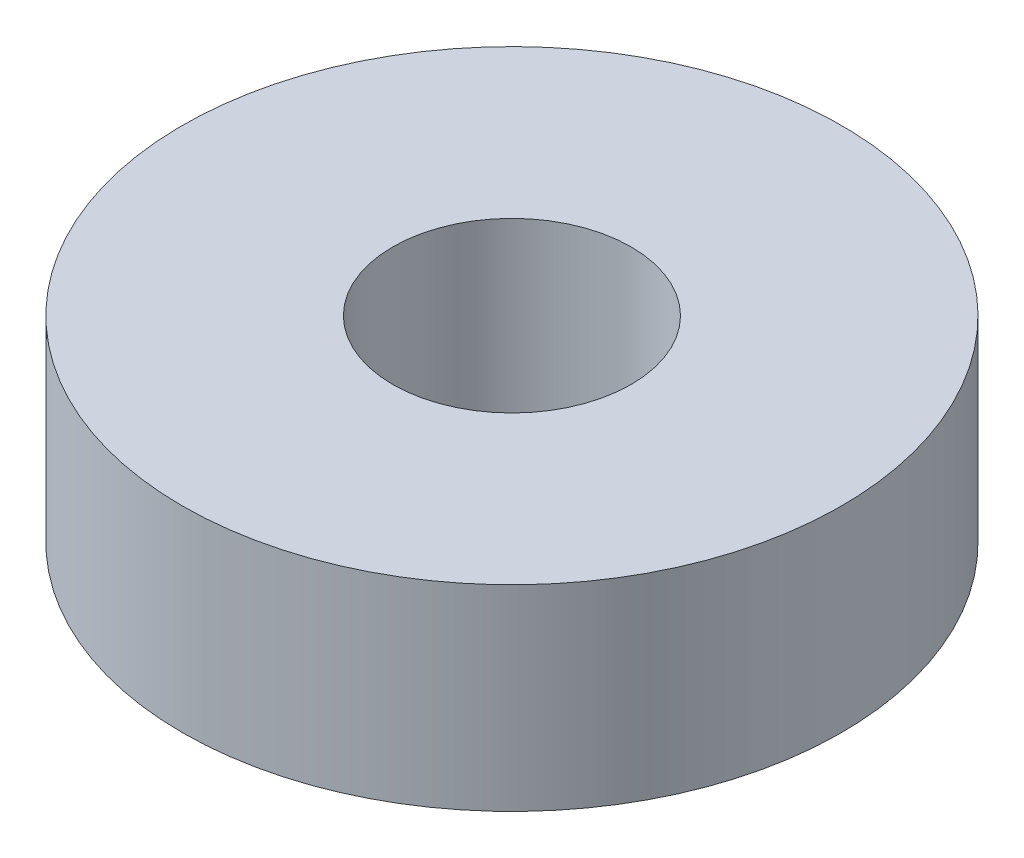
SolidWorks part; units mm, degrees
ref_plane "Front Plane" through (0, 0, 0) normal (0, 0, 1) x (1, 0, 0)
ref_plane "Top Plane" through (0, 0, 0) normal (0, 1, 0) x (1, 0, 0)
ref_plane "Right Plane" through (0, 0, 0) normal (1, 0, 0) x (0, 0, -1)
other "Bounding Box"
ref_plane "Default Plane" through (-8.9266, -12.7485, 0) normal (-0.1736, 0.9848, 0) x (0.9848, 0.1736, 0)
sketch "Sketch1" plane through (0, 0, 0) normal (0, 1, 0) x (1, 0, 0)
  circle A0 centre (0, 0) radius 8.5
  circle A1 centre (0, 0) radius 23.5
  dimension "D1" = 17
  dimension "D2" = 47
extrude "Boss-Extrude1" add sketch "Sketch1" along normal mid plane 14
